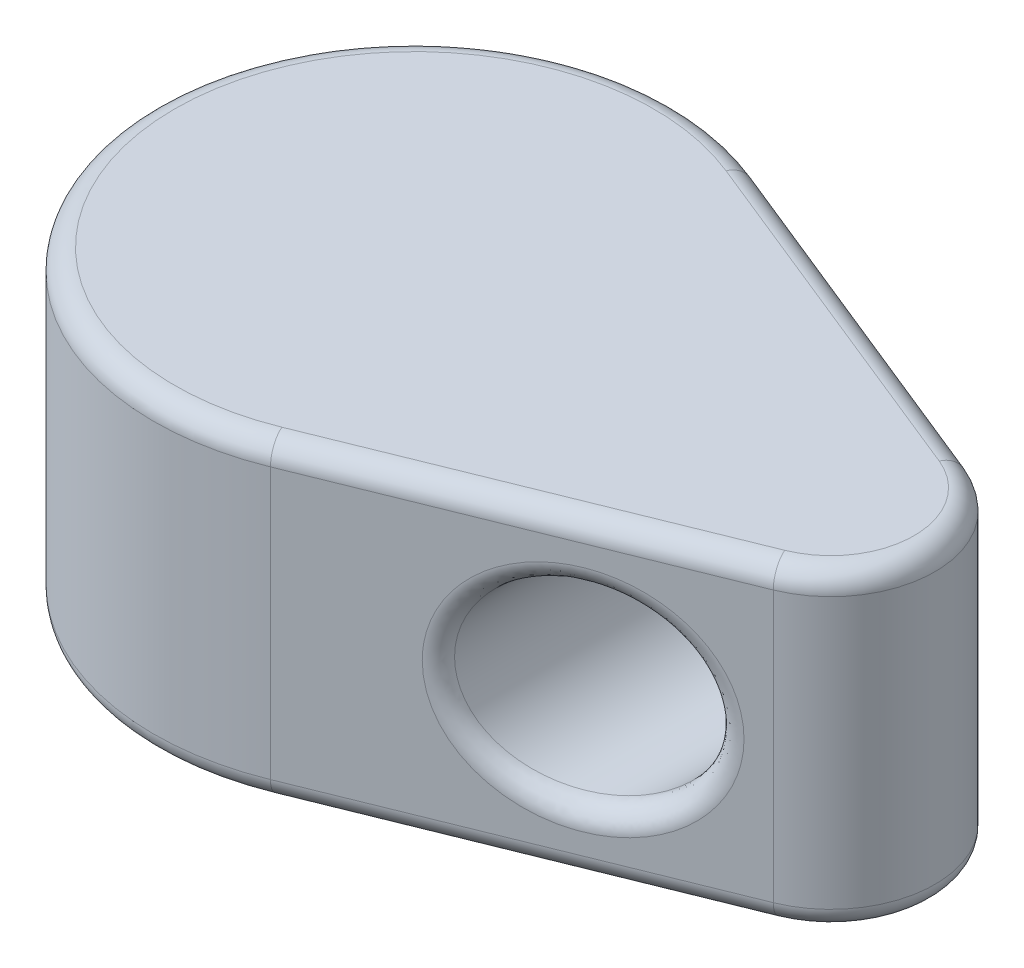
SolidWorks part; units mm, degrees
ref_plane "Front Plane" through (0, 0, 0) normal (0, 0, 1) x (1, 0, 0)
ref_plane "Top Plane" through (0, 0, 0) normal (0, 1, 0) x (1, 0, 0)
ref_plane "Right Plane" through (0, 0, 0) normal (1, 0, 0) x (0, 0, -1)
sketch "Sketch1" plane through (0, 0, 0) normal (0, 1, 0) x (1, 0, 0)
  line L0 (-6.35, 0) -> (12.7, 0) construction
  line L1 (2.3812, 5.8866) -> (11.1125, 2.3546)
  line L2 (11.1125, -2.3546) -> (2.3812, -5.8866)
  circle A0 centre (0, 0) radius 1.016
  circle A1 centre (0, 0) radius 6.35
  circle A2 centre (10.16, 0) radius 2.54
  dimension "D1" = 2.032
  dimension "D2" = 12.7
  dimension "D3" = 19.05
  dimension "D4" = 5.08
extrude "Boss-Extrude1" add sketch "Sketch1" along normal blind 7.62 contours A1 L0 A0 | L0 A1 A0 | A1 L0 A2 L1 | L0 A1 L2 A2 | A2 L0 | L0 A2
sketch "Sketch2" plane through (0, 7.62, 0) normal (0, 1, 0) x (1, 0, 0)
  circle A4 centre (0, 0) radius 1.016 construction
  circle A5 centre (0, 0) radius 1.016
  circle M14 centre (0, 0) radius 1.016
extrude "Boss-Extrude2" add sketch "Sketch2" against normal blind 1.5875 contours M14
sketch "Sketch3" plane through (0, 0, 0) normal (0, 0, 1) x (1, 0, 0)
  line L0 (12.7, 3.81) -> (7.62, 3.81) construction
  line L1 (12.7, 0) -> (12.7, 7.62) construction
  circle A0 centre (7.62, 3.81) radius 2.286
  dimension "D1" = 4.572
  dimension "D2" = 5.08
extrude "Cut-Extrude1" cut sketch "Sketch3" against normal through all both and the other way through all
fillet "Fillet1" radius 0.508 10 edges at (9.906, 3.81, -2.8427) (5.334, 3.81, 4.6922) (6.7469, 0, -4.1206) (12.7, 0, 0) (6.7469, 0, 4.1206) (-6.35, 0, 0) (-6.35, 7.62, 0) (6.7469, 7.62, -4.1206) (12.7, 7.62, 0) (6.7469, 7.62, 4.1206)
fillet "Fillet2" radius 0.127 1 edges at (0, 0, 1.016)
